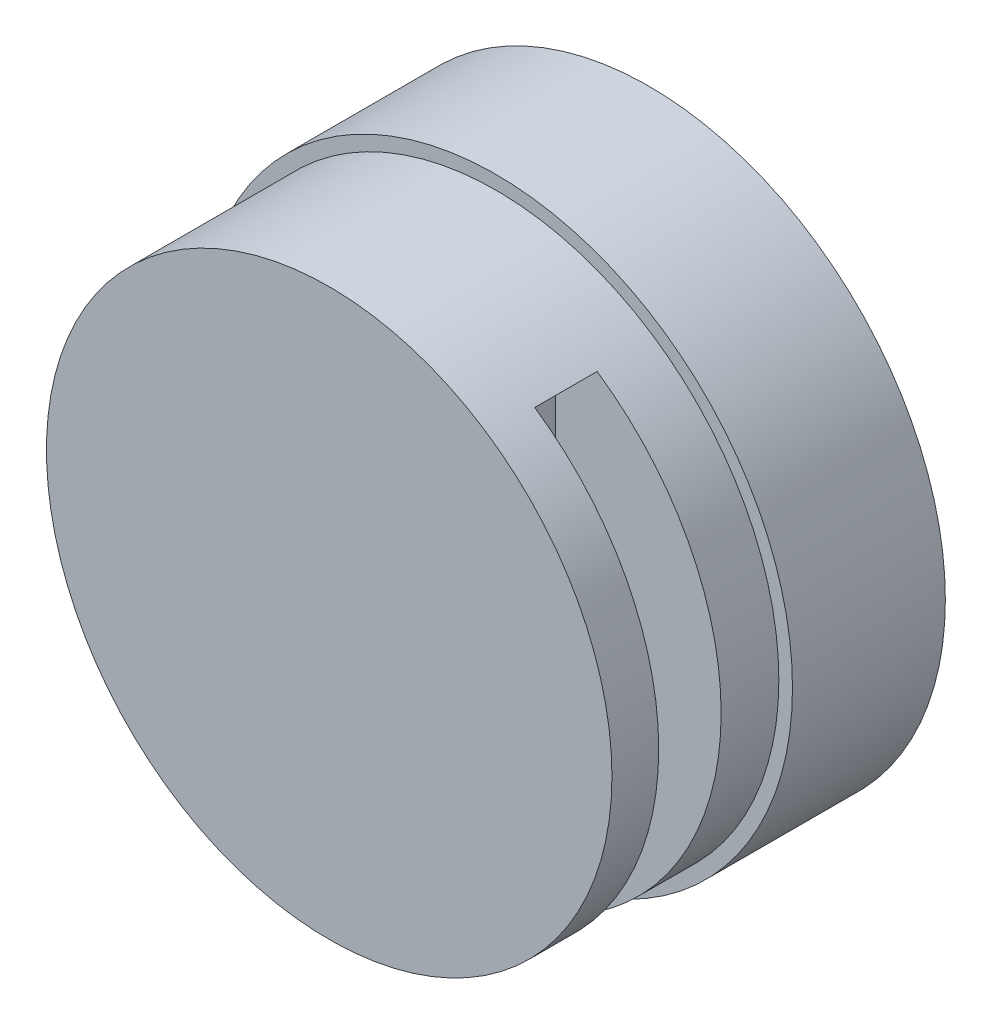
SolidWorks part; units mm, degrees
ref_plane "前视基准面" through (0, 0, 0) normal (0, 0, 1) x (1, 0, 0)
ref_plane "上视基准面" through (0, 0, 0) normal (0, 1, 0) x (1, 0, 0)
ref_plane "右视基准面" through (0, 0, 0) normal (1, 0, 0) x (0, 0, -1)
other "Configuration Table"
sketch "草图1" plane through (0, 0, 0) normal (0, 0, 1) x (1, 0, 0)
  circle A0 centre (0, 0) radius 38
  dimension "D1" = 76
extrude "凸台-拉伸1" add sketch "草图1" along normal blind 19.6
sketch "草图2" plane through (0, 0, 19.6) normal (0, 0, 1) x (1, 0, 0)
  circle A0 centre (0, 0) radius 36.25
  dimension "D1" = 72.5
extrude "凸台-拉伸2" add sketch "草图2" along normal blind 21.4
sketch "草图3" plane through (0, 0, 0) normal (0, 0, -1) x (-1, 0, 0)
  line L0 (-20.8597, 20.8597) -> (20.8597, 20.8597) construction
  circle A0 centre (0, 0) radius 29.5 construction
  circle A2 centre (20.8597, 20.8597) radius 1.5
  circle A3 centre (20.8597, -20.8597) radius 1.5
  circle A4 centre (-20.8597, -20.8597) radius 1.5
  circle A5 centre (-20.8597, 20.8597) radius 1.5
  point P19 (0, 0)
  dimension "D1" = 59
  dimension "D2" = 3
  dimension "D3" = 4
extrude "切除-拉伸1" cut sketch "草图3" against normal blind 4
sketch "草图5" plane through (0, 0, 0) normal (1, 0, 0) x (0, 0, -1)
  line L0 (0, 0) -> (-41, 0) construction
  line L1 (-35, 30) -> (-27, 30)
  line L2 (-35, 30) -> (-35, -30)
  line L3 (-35, -30) -> (-27, -30)
  line L4 (-27, 30) -> (-27, -30)
  line L5 (0, -38) -> (0, 38) construction
  line L6 (-41, 36.25) -> (-41, -36.25) construction
  dimension "D1" = 8
  dimension "D2" = 27
  dimension "D3" = 30
extrude "切除-拉伸2" cut sketch "草图5" along normal up to surface (5.3485 mm away) from offset 15
